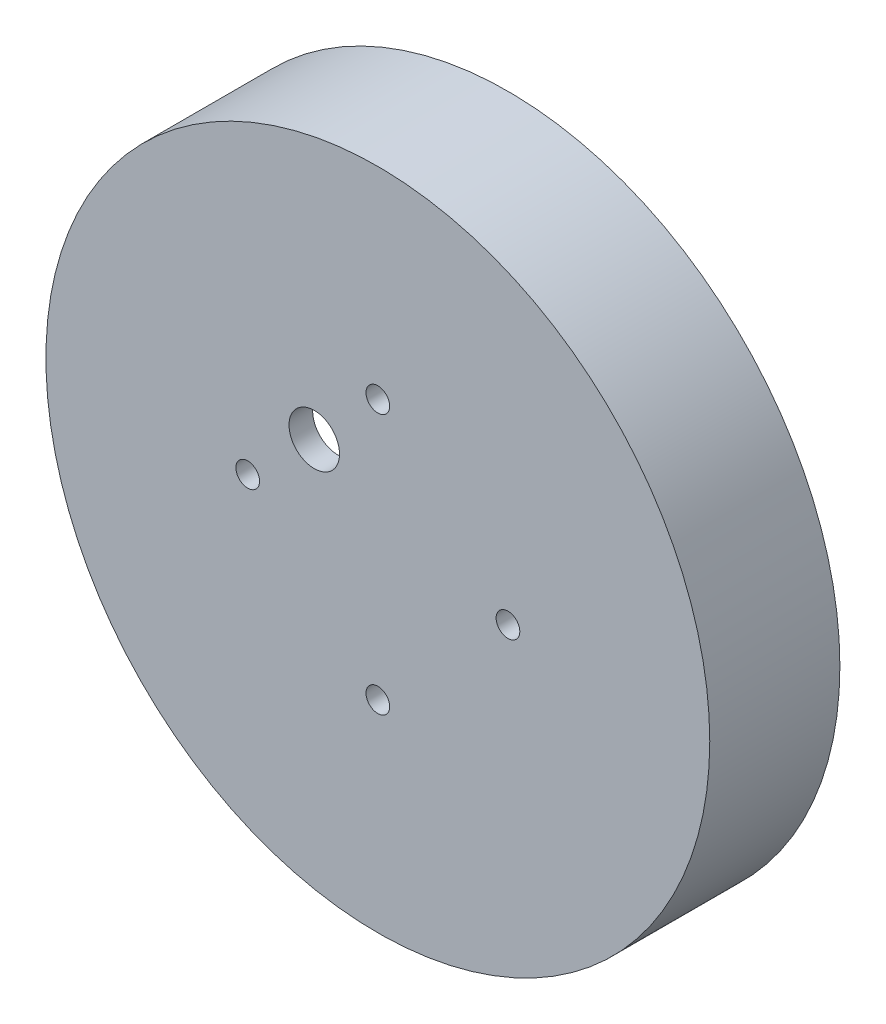
SolidWorks part; units mm, degrees
ref_plane "Front Plane" through (0, 0, 0) normal (0, 0, 1) x (1, 0, 0)
ref_plane "Top Plane" through (0, 0, 0) normal (0, 1, 0) x (1, 0, 0)
ref_plane "Right Plane" through (0, 0, 0) normal (1, 0, 0) x (0, 0, -1)
sketch "Sketch1" plane through (0, 0, -8) normal (0, 0, 1) x (1, 0, 0)
  circle A0 centre (0, 0) radius 38.0875 construction
  circle A1 centre (0, 0) radius 38.0875 construction
  circle A2 centre (0, 0) radius 42.0875
extrude "Boss-Extrude1" add sketch "Sketch1" along normal blind 16.5
sketch "Sketch2" plane through (0, 0, -8) normal (0, 0, -1) x (-1, 0, 0)
  circle A0 centre (0, 0) radius 38.4875
extrude "Cut-Extrude1" cut sketch "Sketch2" against normal offset from surface (8.5 mm away) 8 up to face at (42.0875, 0, 8.5)
sketch "Sketch3" plane through (0, 0, 0.5) normal (0, 0, -1) x (-1, 0, 0)
  circle A0 centre (0, 0) radius 34.4875
extrude "Cut-Extrude2" cut sketch "Sketch3" against normal offset from surface (5 mm away) 3 up to face at (42.0875, 0, 8.5)
sketch "Sketch5" plane through (0, 0, 8.5) normal (0, 0, 1) x (1, 0, 0)
  line L0 (0, 0) -> (-67.0406, 0) construction
  line L1 (0, 0) -> (-50.5565, 50.5565) construction
  circle A0 centre (0, 0) radius 8.2 construction
  circle A1 centre (-8.061, 8.061) radius 3.2
  point P7 (-5.7983, 5.7983)
  point P8 (0, 0)
  point P9 (0, 0)
  point P10 (0, 0)
  point P11 (0, 0)
  dimension "D1" = 16.4
  dimension "D3" = 6.4
  dimension "D2" = 45
extrude "Cut-Extrude4" cut sketch "Sketch5" against normal through all both and the other way through all
sketch "Sketch4" plane through (0, 0, 5.5) normal (0, 0, -1) x (-1, 0, 0)
  line L0 (0, 0) -> (-45.3422, 0) construction
  circle A0 centre (0, 0) radius 15 construction
  circle A1 centre (-16.5, 0) radius 1.5
  point P7 (-15, 0)
  dimension "D1" = 30
  dimension "D2" = 3
extrude "Cut-Extrude3" cut sketch "Sketch4" against normal through all both and the other way through all
pattern_circular "CirPattern1" count 4 over 360 about axis through (0, 0, 0) along (0, 0, 1) of "Cut-Extrude3"
move or copy body "correct side for 3d printing" [suppressed] bodies to move or copy 105 copy no rotation origin (0, 0, 0.25) rotation axis (0, 1, 0) rotation angle 180
equation "\"circ_spline_outer\"= \"D1@Sketch1\""
equation "\"cup_outer_dia\"= \"circ_spline_outer\" + 8mm"
equation "\"cup_inner_dia\"= \"circ_spline_outer\" + 0.8mm"
equation "\"D2@Sketch1\"= \"cup_outer_dia\""
equation "\"outerrunner_height\"= 5.5mm'gap between motor base and rotating sleeve"
equation "\"cup_circ_spline_overlap_height\"= 8mm'height where the motor holding cup fits into the circ spline"
equation "\"motor_holding_plate_height\"= 3mm'back plate of the cup, holding the motor"
equation "\"cup_total_height\"= \"outerrunner_height\" + \"cup_circ_spline_overlap_height\" + \"motor_holding_plate_height\""
equation "\"D1@Sketch2\"= \"cup_inner_dia\""
equation "\"D1@Sketch3\"= \"cup_inner_dia\" - 8"
